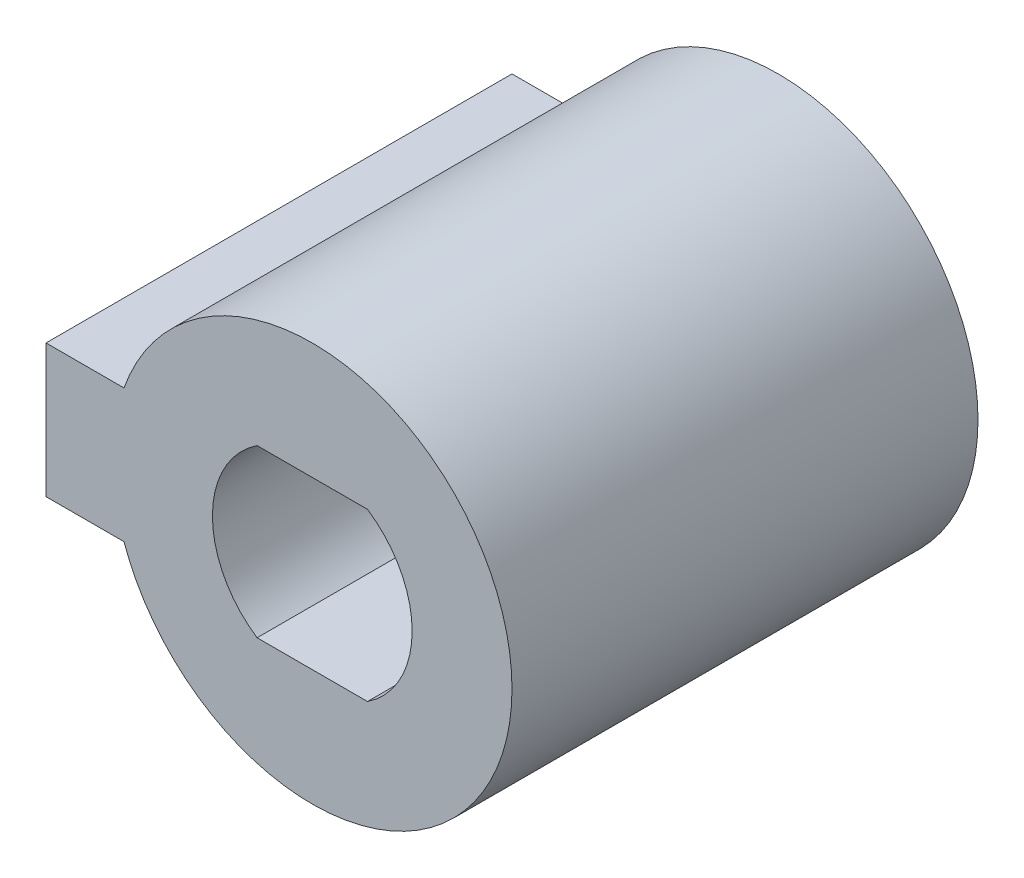
SolidWorks part; units mm, degrees
material "AISI 1020"
ref_plane "Спереди" through (0, 0, 0) normal (0, 0, 1) x (1, 0, 0)
ref_plane "Сверху" through (0, 0, 0) normal (0, 1, 0) x (1, 0, 0)
ref_plane "Справа" through (0, 0, 0) normal (1, 0, 0) x (0, 0, -1)
sketch "Эскиз1" plane through (0, 0, 0) normal (0, 0, 1) x (1, 0, 0)
  line L0 (3.3166, 5) -> (-3.3166, 5)
  line L1 (-3.3166, -5) -> (3.3166, -5)
  line L2 (-11.3137, 4) -> (-16, 4)
  line L3 (-16, 4) -> (-16, -4)
  line L4 (-16, -4) -> (-11.3137, -4)
  line L5 (-12, 4) -> (-12, -4) construction
  arc A0 (-11.3137, -4) -> (-11.3137, 4) centre (0, 0) ccw
  circle A1 centre (0, 0) radius 6 construction
  arc A2 (-3.3166, 5) -> (-3.3166, -5) centre (0, 0) ccw
  arc A3 (3.3166, -5) -> (3.3166, 5) centre (0, 0) ccw
  point P15 (-12, 0)
  dimension "D1" = 24
  dimension "D2" = 10
  dimension "D3" = 8
  dimension "D4" = 4
extrude "Бобышка-Вытянуть1" add sketch "Эскиз1" along normal offset from surface 5 and the other way blind 1
